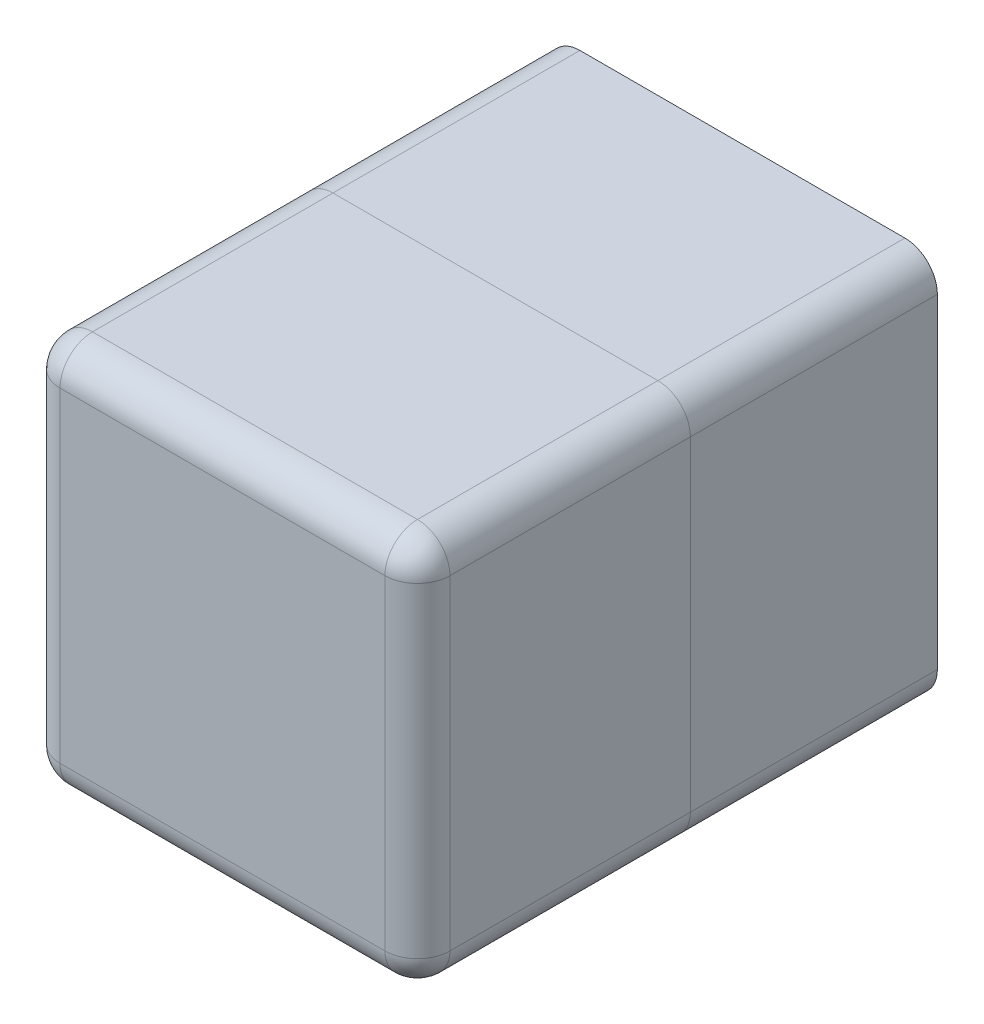
SolidWorks part; units mm, degrees
material "1023 Carbon Steel Sheet (SS)"
ref_plane "Front Plane" through (0, 0, 0) normal (0, 0, 1) x (1, 0, 0)
ref_plane "Top Plane" through (0, 0, 0) normal (0, 1, 0) x (1, 0, 0)
ref_plane "Right Plane" through (0, 0, 0) normal (1, 0, 0) x (0, 0, -1)
sketch "Sketch2" plane through (0, 0, 0) normal (0, 0, 1) x (1, 0, 0)
  line L1 (0, 0) -> (60, 0)
  line L2 (0, 0) -> (0, 60)
  line L3 (0, 60) -> (60, 60)
  line L4 (60, 0) -> (60, 60)
  dimension "D1" = 60
  dimension "D2" = 60
extrude "Boss-Extrude1" add sketch "Sketch2" along normal blind 42
sketch "Sketch3" plane through (0, 0, 0) normal (0, 0, -1) x (-1, 0, 0)
  line L4 (0, 0) -> (0, 60)
  line L5 (0, 60) -> (-60, 60)
  line L6 (-60, 60) -> (-60, 0)
  line L7 (-60, 0) -> (0, 0)
  line L8 (0, 0) -> (0, 60)
  line L9 (0, 60) -> (-60, 60)
  line L10 (-60, 60) -> (-60, 0)
  line L11 (-60, 0) -> (0, 0)
  dimension "D1" = 0
extrude "Boss-Extrude2" add sketch "Sketch3" along normal blind 38 separate body
fillet "Fillet1" radius 5 4 edges at (0, 0, 21) (60, 0, 21) (0, 60, 21) (60, 60, 21)
fillet "Fillet2" radius 5 4 edges at (0, 0, -19) (60, 0, -19) (60, 60, -19) (0, 60, -19)
fillet "Fillet3" radius 5 8 edges at (1.4645, 1.4645, 42) (0, 30, 42) (1.4645, 58.5355, 42) (30, 60, 42) (58.5355, 58.5355, 42) (60, 30, 42) (58.5355, 1.4645, 42) (30, 0, 42)
sketch "Sketch4" plane through (0, 0, -38) normal (0, 0, -1) x (-1, 0, 0)
  line L0 (-30, 60) -> (-30, 0) construction
  line L1 (-5, 60) -> (-55, 60) construction
  line L2 (-55, 0) -> (-5, 0) construction
  line L3 (-30, 30) -> (-1.4645, 58.5355) construction
  line L4 (-30, 30) -> (5, 30) construction
  circle A0 centre (-30, 30) radius 35 construction
  arc A1 (0, 55) -> (-5, 60) centre (-5, 55) ccw construction
  circle A2 centre (-5.2513, 54.7487) radius 2.25
  circle A3 centre (-54.7487, 54.7487) radius 2.25
  circle A4 centre (-54.7487, 5.2513) radius 2.25
  circle A5 centre (-5.2513, 5.2513) radius 2.25
  dimension "D1" = 70
  dimension "D2" = 4.5
extrude "Cut-Extrude1" cut sketch "Sketch4" against normal blind 10
sketch "Sketch5" plane through (0, 0, -38) normal (0, 0, -1) x (-1, 0, 0)
  line L0 (-30, 60) -> (-30, 0) construction
  line L1 (-5, 60) -> (-55, 60) construction
  line L2 (-55, 0) -> (-5, 0) construction
  line L3 (-30, 30) -> (0, 30) construction
  line L4 (0, 5) -> (0, 55) construction
  line L5 (0, 55) -> (0, 5) construction
  circle A0 centre (-30, 40) radius 12
  point P14 (-30, 28)
  point P18 (0, 30)
  dimension "D1" = 24
  dimension "D2" = 2
extrude "Boss-Extrude3" add sketch "Sketch5" along normal blind 4
sketch "Sketch6" plane through (0, 0, -42) normal (0, 0, -1) x (-1, 0, 0)
  line L0 (-30, 28) -> (-30, 40) construction
  circle A0 centre (-30, 40) radius 12 construction
  circle A1 centre (-30, 40) radius 5
  dimension "D2" = 10
  dimension "D1" = 12
extrude "Boss-Extrude4" add sketch "Sketch6" along normal blind 28 contours A1
ref_plane "Plane1" through (0, 42.5, 0) normal (0, 1, 0) x (1, 0, 0)
sketch "Sketch7" plane through (0, 42.5, 0) normal (0, 1, 0) x (1, 0, 0)
  line L0 (30, 70) -> (30, 45) construction
  line L1 (35, 70) -> (25, 70) construction
  line L2 (28, 47) -> (28, 70)
  line L3 (28, 70) -> (32, 70)
  line L4 (32, 70) -> (32, 47)
  arc A0 (28, 47) -> (32, 47) centre (30, 47) ccw
  dimension "D2" = 4
  dimension "D1" = 25
extrude "Cut-Extrude2" cut sketch "Sketch7" along normal blind 28
ref_plane "Plane2" through (30, 0, 0) normal (-1, 0, 0) x (0, 0, 1)
sketch "Sketch8" plane through (0, 0, -70) normal (0, 0, -1) x (-1, 0, 0)
  circle A0 centre (-30, 40) radius 5
extrude "Cut-Extrude3" cut sketch "Sketch8" against normal blind 33
